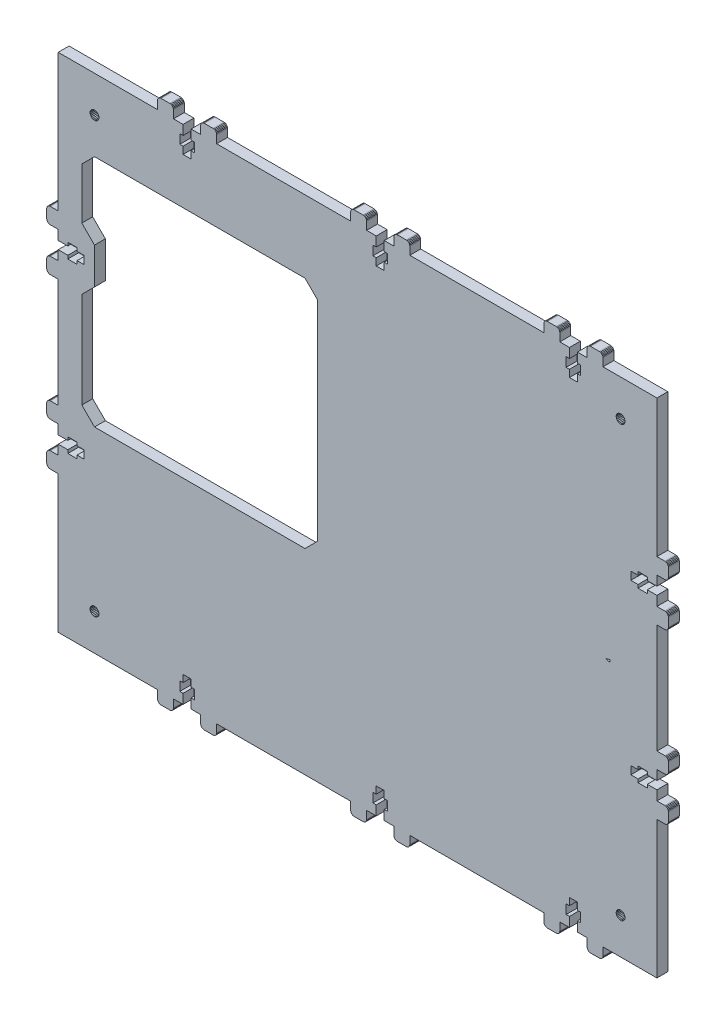
SolidWorks part; units mm, degrees
material "Maple"
ref_plane "Front Plane" through (0, 0, 0) normal (0, 0, 1) x (1, 0, 0)
ref_plane "Top Plane" through (0, 0, 0) normal (0, 1, 0) x (1, 0, 0)
ref_plane "Right Plane" through (0, 0, 0) normal (1, 0, 0) x (0, 0, -1)
sketch "Sketch1" plane through (0, 0, 0) normal (0, 0, 1) x (1, 0, 0)
  line L4138 (-90.633, 287.9777) -> (-85.333, 287.9777)
  line L4139 (-95.733, 287.9777) -> (-95.733, 286.1777)
  line L4140 (-90.633, 286.1777) -> (-90.633, 287.9777)
  line L4141 (-90.633, 294.1777) -> (-95.733, 294.1777)
  line L4142 (-415.2329, 189.8778) -> (-415.2329, 195.1777)
  line L4143 (-95.733, 292.3777) -> (-99.683, 292.3777)
  line L4144 (-147.633, 105.3778) -> (-221.483, 105.3778)
  line L4145 (-346.4329, 376.8777) -> (-348.2329, 376.8777)
  line L4146 (-342.0329, 367.8277) -> (-342.0329, 371.7777)
  line L4147 (-348.2329, 371.7777) -> (-346.4329, 371.7777)
  line L4148 (-336.7329, 382.1777) -> (-336.7329, 386.5277)
  line L4149 (-360.5329, 382.1777) -> (-360.5329, 386.5277)
  line L4150 (-340.2329, 371.7777) -> (-340.2329, 376.8777)
  line L4151 (-346.4329, 367.8277) -> (-342.0329, 367.8277)
  line L4152 (-90.633, 195.1777) -> (-85.333, 195.1777)
  line L4153 (-254.083, 105.3778) -> (-327.933, 105.3778)
  line L4154 (-85.333, 199.5777) -> (-90.633, 199.5777)
  line L4155 (-129.133, 371.7777) -> (-127.333, 371.7777)
  line L4156 (-95.733, 195.1777) -> (-95.733, 193.3777)
  line L4157 (-85.333, 292.3777) -> (-90.633, 292.3777)
  line L4158 (-133.533, 367.8277) -> (-129.133, 367.8277)
  line L4159 (-90.633, 201.3777) -> (-95.733, 201.3777)
  line L4160 (-340.2329, 376.8777) -> (-342.0329, 376.8777)
  line L4161 (-348.2329, 376.8777) -> (-348.2329, 371.7777)
  line L4162 (-415.2329, 382.1777) -> (-360.5329, 382.1777)
  line L4163 (-135.333, 371.7777) -> (-133.533, 371.7777)
  line L4164 (-415.2329, 105.3778) -> (-415.2329, 181.0778)
  line L4165 (-239.983, 371.7777) -> (-239.983, 367.8277)
  line L4166 (-235.583, 367.8277) -> (-235.583, 371.7777)
  line L4167 (-127.333, 110.6778) -> (-127.333, 115.7778)
  line L4168 (-129.133, 110.6778) -> (-127.333, 110.6778)
  line L4169 (-133.533, 119.7278) -> (-133.533, 115.7778)
  line L4170 (-135.333, 376.8777) -> (-135.333, 371.7777)
  line L4171 (-409.9329, 286.1777) -> (-404.8329, 286.1777)
  line L4172 (-409.9329, 287.9777) -> (-409.9329, 286.1777)
  line L4173 (-400.8829, 292.3777) -> (-404.8329, 292.3777)
  line L4174 (-404.8329, 286.1777) -> (-404.8329, 287.9777)
  line L4175 (-415.2329, 297.6777) -> (-419.5829, 297.6777)
  line L4176 (-415.2329, 273.8777) -> (-419.5829, 273.8777)
  line L4177 (-404.8329, 294.1777) -> (-409.9329, 294.1777)
  line L4178 (-230.283, 382.1777) -> (-230.283, 386.5277)
  line L4179 (-360.5329, 105.3778) -> (-415.2329, 105.3778)
  line L4180 (-409.9329, 292.3777) -> (-415.2329, 292.3777)
  line L4181 (-404.8329, 292.3777) -> (-404.8329, 294.1777)
  line L4182 (-409.9329, 294.1777) -> (-409.9329, 292.3777)
  line L4183 (-115.033, 382.1777) -> (-85.333, 382.1777)
  line L4184 (-239.983, 382.1777) -> (-239.983, 376.8777)
  line L4185 (-235.583, 376.8777) -> (-235.583, 382.1777)
  line L4186 (-241.783, 376.8777) -> (-241.783, 371.7777)
  line L4187 (-409.9329, 193.3777) -> (-404.8329, 193.3777)
  line L4188 (-409.9329, 195.1777) -> (-409.9329, 193.3777)
  line L4189 (-400.8829, 199.5777) -> (-404.8329, 199.5777)
  line L4190 (-127.333, 115.7778) -> (-129.133, 115.7778)
  line L4191 (-138.833, 105.3778) -> (-138.833, 101.0278)
  line L4192 (-115.033, 105.3778) -> (-115.033, 101.0278)
  line L4193 (-135.333, 115.7778) -> (-135.333, 110.6778)
  line L4194 (-129.133, 119.7278) -> (-133.533, 119.7278)
  line L4195 (-346.4329, 119.7278) -> (-346.4329, 115.7778)
  line L4196 (-235.583, 119.7278) -> (-239.983, 119.7278)
  line L4197 (-415.2329, 306.4777) -> (-415.2329, 382.1777)
  line L4198 (-235.583, 105.3778) -> (-235.583, 110.6778)
  line L4199 (-133.533, 105.3778) -> (-138.833, 105.3778)
  line L4200 (-123.833, 105.3778) -> (-129.133, 105.3778)
  line L4201 (-133.533, 115.7778) -> (-135.333, 115.7778)
  line L4202 (-135.333, 110.6778) -> (-133.533, 110.6778)
  line L4203 (-235.583, 115.7778) -> (-235.583, 119.7278)
  line L4204 (-230.283, 105.3778) -> (-235.583, 105.3778)
  line L4205 (-90.633, 193.3777) -> (-90.633, 195.1777)
  line L4206 (-346.4329, 110.6778) -> (-346.4329, 105.3778)
  line L4207 (-346.4329, 115.7778) -> (-348.2329, 115.7778)
  line L4208 (-85.333, 213.6777) -> (-80.983, 213.6777)
  line L4209 (-95.733, 193.3777) -> (-90.633, 193.3777)
  line L4210 (-90.633, 199.5777) -> (-90.633, 201.3777)
  line L4211 (-342.0329, 376.8777) -> (-342.0329, 382.1777)
  line L4212 (-342.0329, 371.7777) -> (-340.2329, 371.7777)
  line L4213 (-351.7329, 105.3778) -> (-351.7329, 101.0278)
  line L4214 (-327.933, 105.3778) -> (-327.933, 101.0278)
  line L4215 (-348.2329, 115.7778) -> (-348.2329, 110.6778)
  line L4216 (-127.333, 371.7777) -> (-127.333, 376.8777)
  line L4217 (-415.2329, 195.1777) -> (-409.9329, 195.1777)
  line L4218 (-235.583, 382.1777) -> (-230.283, 382.1777)
  line L4219 (-241.783, 371.7777) -> (-239.983, 371.7777)
  line L4220 (-239.983, 376.8777) -> (-241.783, 376.8777)
  line L4221 (-346.4329, 382.1777) -> (-346.4329, 376.8777)
  line L4222 (-346.4329, 371.7777) -> (-346.4329, 367.8277)
  line L4223 (-239.983, 110.6778) -> (-239.983, 105.3778)
  line L4224 (-239.983, 115.7778) -> (-241.783, 115.7778)
  line L4225 (-241.783, 110.6778) -> (-239.983, 110.6778)
  line L4226 (-233.783, 110.6778) -> (-233.783, 115.7778)
  line L4227 (-415.2329, 292.3777) -> (-415.2329, 297.6777)
  line L4228 (-415.2329, 199.5777) -> (-415.2329, 204.8777)
  line L4229 (-133.533, 376.8777) -> (-135.333, 376.8777)
  line L4230 (-404.8329, 193.3777) -> (-404.8329, 195.1777)
  line L4231 (-415.2329, 287.9777) -> (-409.9329, 287.9777)
  line L4232 (-404.8329, 287.9777) -> (-400.8829, 287.9777)
  line L4233 (-415.2329, 282.6777) -> (-415.2329, 287.9777)
  line L4234 (-239.983, 367.8277) -> (-235.583, 367.8277)
  line L4235 (-233.783, 376.8777) -> (-235.583, 376.8777)
  line L4236 (-233.783, 371.7777) -> (-233.783, 376.8777)
  line L4237 (-346.4329, 105.3778) -> (-351.7329, 105.3778)
  line L4238 (-340.2329, 110.6778) -> (-340.2329, 115.7778)
  line L4239 (-90.633, 292.3777) -> (-90.633, 294.1777)
  line L4240 (-99.683, 287.9777) -> (-95.733, 287.9777)
  line L4241 (-95.733, 294.1777) -> (-95.733, 292.3777)
  line L4242 (-85.333, 282.6777) -> (-80.983, 282.6777)
  line L4243 (-85.333, 195.1777) -> (-85.333, 189.8777)
  line L4244 (-400.8829, 287.9777) -> (-400.8829, 292.3777)
  line L4245 (-133.533, 382.1777) -> (-133.533, 376.8777)
  line L4246 (-133.533, 371.7777) -> (-133.533, 367.8277)
  line L4247 (-129.133, 367.8277) -> (-129.133, 371.7777)
  line L4248 (-342.0329, 382.1777) -> (-336.7329, 382.1777)
  line L4249 (-327.9329, 382.1777) -> (-254.083, 382.1777)
  line L4250 (-221.483, 382.1777) -> (-147.633, 382.1777)
  line L4251 (-351.7329, 382.1777) -> (-346.4329, 382.1777)
  line L4252 (-404.8329, 201.3777) -> (-409.9329, 201.3777)
  line L4253 (-400.8829, 195.1777) -> (-400.8829, 199.5777)
  line L4254 (-409.9329, 199.5777) -> (-415.2329, 199.5777)
  line L4255 (-239.983, 119.7278) -> (-239.983, 115.7778)
  line L4256 (-233.783, 115.7778) -> (-235.583, 115.7778)
  line L4257 (-245.283, 105.3778) -> (-245.283, 101.0278)
  line L4258 (-221.483, 105.3778) -> (-221.483, 101.0278)
  line L4259 (-241.783, 115.7778) -> (-241.783, 110.6778)
  line L4260 (-95.733, 286.1777) -> (-90.633, 286.1777)
  line L4261 (-99.683, 292.3777) -> (-99.683, 287.9777)
  line L4262 (-415.2329, 204.8777) -> (-419.5829, 204.8777)
  line L4263 (-415.2329, 181.0778) -> (-419.5829, 181.0778)
  line L4264 (-99.683, 195.1777) -> (-95.733, 195.1777)
  line L4265 (-85.333, 189.8777) -> (-80.983, 189.8777)
  line L4266 (-245.283, 382.1777) -> (-239.983, 382.1777)
  line L4267 (-129.133, 105.3778) -> (-129.133, 110.6778)
  line L4268 (-129.133, 115.7778) -> (-129.133, 119.7278)
  line L4269 (-239.983, 105.3778) -> (-245.283, 105.3778)
  line L4270 (-133.533, 110.6778) -> (-133.533, 105.3778)
  line L4271 (-235.583, 371.7777) -> (-233.783, 371.7777)
  line L4272 (-336.7329, 105.3778) -> (-342.0329, 105.3778)
  line L4273 (-404.8329, 195.1777) -> (-400.8829, 195.1777)
  line L4274 (-85.333, 287.9777) -> (-85.333, 282.6777)
  line L4275 (-85.333, 273.8777) -> (-85.333, 213.6777)
  line L4276 (-85.333, 204.8777) -> (-85.333, 199.5777)
  line L4277 (-254.083, 382.1777) -> (-254.083, 386.5277)
  line L4278 (-409.9329, 201.3777) -> (-409.9329, 199.5777)
  line L4279 (-127.333, 376.8777) -> (-129.133, 376.8777)
  line L4280 (-129.133, 376.8777) -> (-129.133, 382.1777)
  line L4281 (-129.133, 382.1777) -> (-123.833, 382.1777)
  line L4282 (-415.2329, 213.6777) -> (-415.2329, 273.8777)
  line L4283 (-123.833, 382.1777) -> (-123.833, 386.5277)
  line L4284 (-85.333, 181.0778) -> (-85.333, 105.3778)
  line L4285 (-85.333, 105.3778) -> (-115.033, 105.3778)
  line L4286 (-95.733, 201.3777) -> (-95.733, 199.5777)
  line L4287 (-95.733, 199.5777) -> (-99.683, 199.5777)
  line L4288 (-99.683, 199.5777) -> (-99.683, 195.1777)
  line L4289 (-342.0329, 105.3778) -> (-342.0329, 110.6778)
  line L4290 (-342.0329, 110.6778) -> (-340.2329, 110.6778)
  line L4291 (-340.2329, 115.7778) -> (-342.0329, 115.7778)
  line L4292 (-342.0329, 115.7778) -> (-342.0329, 119.7278)
  line L4293 (-342.0329, 119.7278) -> (-346.4329, 119.7278)
  line L4294 (-404.8329, 199.5777) -> (-404.8329, 201.3777)
  line L4295 (-85.333, 382.1777) -> (-85.333, 306.4777)
  line L4296 (-85.333, 306.4777) -> (-80.983, 306.4777)
  line L4297 (-78.983, 299.6777) -> (-79.0512, 299.1601)
  line L4298 (-79.0512, 299.1601) -> (-79.251, 298.6777)
  line L4299 (-79.251, 298.6777) -> (-79.5688, 298.2635)
  line L4300 (-79.5688, 298.2635) -> (-79.983, 297.9457)
  line L4301 (-79.983, 297.9457) -> (-80.4654, 297.7459)
  line L4302 (-80.983, 297.6777) -> (-85.333, 297.6777)
  line L4303 (-80.4654, 297.7459) -> (-80.983, 297.6777)
  line L4304 (-80.983, 282.6777) -> (-80.4654, 282.6096)
  line L4305 (-80.4654, 282.6096) -> (-79.983, 282.4098)
  line L4306 (-79.983, 282.4098) -> (-79.5688, 282.0919)
  line L4307 (-79.5688, 282.0919) -> (-79.251, 281.6777)
  line L4308 (-79.251, 281.6777) -> (-79.0512, 281.1954)
  line L4309 (-78.983, 280.6777) -> (-78.983, 275.8777)
  line L4310 (-79.0512, 281.1954) -> (-78.983, 280.6777)
  line L4311 (-80.983, 273.8777) -> (-85.333, 273.8777)
  line L4312 (-80.983, 273.8777) -> (-80.4654, 273.9459)
  line L4313 (-80.4654, 273.9459) -> (-79.983, 274.1457)
  line L4314 (-79.983, 274.1457) -> (-79.5688, 274.4635)
  line L4315 (-79.5688, 274.4635) -> (-79.251, 274.8777)
  line L4316 (-79.251, 274.8777) -> (-79.0512, 275.3601)
  line L4317 (-79.0512, 275.3601) -> (-78.983, 275.8777)
  line L4318 (-80.983, 306.4777) -> (-80.4654, 306.4096)
  line L4319 (-80.4654, 306.4096) -> (-79.983, 306.2098)
  line L4320 (-79.983, 306.2098) -> (-79.5688, 305.8919)
  line L4321 (-79.5688, 305.8919) -> (-79.251, 305.4777)
  line L4322 (-79.251, 305.4777) -> (-79.0512, 304.9953)
  line L4323 (-78.983, 304.4777) -> (-78.983, 299.6777)
  line L4324 (-79.0512, 304.9953) -> (-78.983, 304.4777)
  line L4325 (-80.983, 189.8777) -> (-80.4654, 189.8096)
  line L4326 (-80.4654, 189.8096) -> (-79.983, 189.6098)
  line L4327 (-79.983, 189.6098) -> (-79.5688, 189.292)
  line L4328 (-79.5688, 189.292) -> (-79.251, 188.8777)
  line L4329 (-79.251, 188.8777) -> (-79.0512, 188.3954)
  line L4330 (-78.983, 187.8777) -> (-78.983, 183.0778)
  line L4331 (-79.0512, 188.3954) -> (-78.983, 187.8777)
  line L4332 (-80.983, 181.0778) -> (-85.333, 181.0778)
  line L4333 (-80.983, 181.0778) -> (-80.4654, 181.1459)
  line L4334 (-80.4654, 181.1459) -> (-79.983, 181.3457)
  line L4335 (-79.983, 181.3457) -> (-79.5688, 181.6635)
  line L4336 (-79.5688, 181.6635) -> (-79.251, 182.0778)
  line L4337 (-79.251, 182.0778) -> (-79.0512, 182.5601)
  line L4338 (-79.0512, 182.5601) -> (-78.983, 183.0778)
  line L4339 (-80.983, 204.8777) -> (-85.333, 204.8777)
  line L4340 (-80.983, 204.8777) -> (-80.4654, 204.9459)
  line L4341 (-80.4654, 204.9459) -> (-79.983, 205.1457)
  line L4342 (-79.983, 205.1457) -> (-79.5688, 205.4635)
  line L4343 (-79.5688, 205.4635) -> (-79.251, 205.8777)
  line L4344 (-79.251, 205.8777) -> (-79.0512, 206.3601)
  line L4345 (-79.0512, 206.3601) -> (-78.983, 206.8777)
  line L4346 (-80.983, 213.6777) -> (-80.4654, 213.6096)
  line L4347 (-80.4654, 213.6096) -> (-79.983, 213.4098)
  line L4348 (-79.983, 213.4098) -> (-79.5688, 213.092)
  line L4349 (-79.5688, 213.092) -> (-79.251, 212.6777)
  line L4350 (-79.251, 212.6777) -> (-79.0512, 212.1954)
  line L4351 (-78.983, 211.6777) -> (-78.983, 206.8777)
  line L4352 (-79.0512, 212.1954) -> (-78.983, 211.6777)
  line L4353 (-419.5829, 213.6777) -> (-415.2329, 213.6777)
  line L4354 (-419.5829, 213.6777) -> (-420.1006, 213.6096)
  line L4355 (-420.1006, 213.6096) -> (-420.5829, 213.4098)
  line L4356 (-420.5829, 213.4098) -> (-420.9971, 213.092)
  line L4357 (-420.9971, 213.092) -> (-421.315, 212.6777)
  line L4358 (-421.315, 212.6777) -> (-421.5148, 212.1954)
  line L4359 (-421.5148, 212.1954) -> (-421.5829, 211.6777)
  line L4360 (-419.5829, 204.8777) -> (-420.1006, 204.9459)
  line L4361 (-420.1006, 204.9459) -> (-420.5829, 205.1457)
  line L4362 (-420.5829, 205.1457) -> (-420.9971, 205.4635)
  line L4363 (-420.9971, 205.4635) -> (-421.315, 205.8777)
  line L4364 (-421.315, 205.8777) -> (-421.5148, 206.3601)
  line L4365 (-421.5829, 206.8777) -> (-421.5829, 211.6777)
  line L4366 (-421.5148, 206.3601) -> (-421.5829, 206.8777)
  line L4367 (-254.083, 101.0278) -> (-254.083, 105.3778)
  line L4368 (-254.083, 101.0278) -> (-254.0148, 100.5101)
  line L4369 (-254.0148, 100.5101) -> (-253.815, 100.0278)
  line L4370 (-253.815, 100.0278) -> (-253.4972, 99.6136)
  line L4371 (-253.4972, 99.6136) -> (-253.083, 99.2957)
  line L4372 (-253.083, 99.2957) -> (-252.6006, 99.0959)
  line L4373 (-252.6006, 99.0959) -> (-252.083, 99.0278)
  line L4374 (-334.7329, 99.0278) -> (-335.2506, 99.0959)
  line L4375 (-335.2506, 99.0959) -> (-335.7329, 99.2957)
  line L4376 (-335.7329, 99.2957) -> (-336.1472, 99.6136)
  line L4377 (-336.1472, 99.6136) -> (-336.465, 100.0278)
  line L4378 (-336.465, 100.0278) -> (-336.6648, 100.5101)
  line L4379 (-336.7329, 101.0278) -> (-336.7329, 105.3778)
  line L4380 (-336.6648, 100.5101) -> (-336.7329, 101.0278)
  line L4381 (-334.7329, 388.5277) -> (-329.9329, 388.5277)
  line L4382 (-334.7329, 388.5277) -> (-335.2506, 388.4595)
  line L4383 (-335.2506, 388.4595) -> (-335.7329, 388.2597)
  line L4384 (-335.7329, 388.2597) -> (-336.1472, 387.9419)
  line L4385 (-336.1472, 387.9419) -> (-336.465, 387.5277)
  line L4386 (-336.465, 387.5277) -> (-336.6648, 387.0453)
  line L4387 (-336.6648, 387.0453) -> (-336.7329, 386.5277)
  line L4388 (-360.5329, 386.5277) -> (-360.4648, 387.0453)
  line L4389 (-360.4648, 387.0453) -> (-360.265, 387.5277)
  line L4390 (-360.265, 387.5277) -> (-359.9471, 387.9419)
  line L4391 (-359.9471, 387.9419) -> (-359.5329, 388.2597)
  line L4392 (-359.5329, 388.2597) -> (-359.0506, 388.4595)
  line L4393 (-358.5329, 388.5277) -> (-353.7329, 388.5277)
  line L4394 (-359.0506, 388.4595) -> (-358.5329, 388.5277)
  line L4395 (-351.7329, 386.5277) -> (-351.7329, 382.1777)
  line L4396 (-351.7329, 386.5277) -> (-351.8011, 387.0453)
  line L4397 (-351.8011, 387.0453) -> (-352.0009, 387.5277)
  line L4398 (-352.0009, 387.5277) -> (-352.3187, 387.9419)
  line L4399 (-352.3187, 387.9419) -> (-352.7329, 388.2597)
  line L4400 (-352.7329, 388.2597) -> (-353.2153, 388.4595)
  line L4401 (-353.2153, 388.4595) -> (-353.7329, 388.5277)
  line L4402 (-121.833, 388.5277) -> (-117.033, 388.5277)
  line L4403 (-121.833, 388.5277) -> (-122.3506, 388.4595)
  line L4404 (-122.3506, 388.4595) -> (-122.833, 388.2597)
  line L4405 (-122.833, 388.2597) -> (-123.2472, 387.9419)
  line L4406 (-123.2472, 387.9419) -> (-123.5651, 387.5277)
  line L4407 (-123.5651, 387.5277) -> (-123.7649, 387.0453)
  line L4408 (-123.7649, 387.0453) -> (-123.833, 386.5277)
  line L4409 (-358.5329, 99.0278) -> (-359.0506, 99.0959)
  line L4410 (-359.0506, 99.0959) -> (-359.5329, 99.2957)
  line L4411 (-359.5329, 99.2957) -> (-359.9471, 99.6136)
  line L4412 (-359.9471, 99.6136) -> (-360.265, 100.0278)
  line L4413 (-360.265, 100.0278) -> (-360.4648, 100.5101)
  line L4414 (-360.5329, 101.0278) -> (-360.5329, 105.3778)
  line L4415 (-360.4648, 100.5101) -> (-360.5329, 101.0278)
  line L4416 (-421.5829, 299.6777) -> (-421.5829, 304.4777)
  line L4417 (-421.5829, 299.6777) -> (-421.5148, 299.1601)
  line L4418 (-421.5148, 299.1601) -> (-421.315, 298.6777)
  line L4419 (-421.315, 298.6777) -> (-420.9971, 298.2635)
  line L4420 (-420.9971, 298.2635) -> (-420.5829, 297.9457)
  line L4421 (-420.5829, 297.9457) -> (-420.1006, 297.7459)
  line L4422 (-420.1006, 297.7459) -> (-419.5829, 297.6777)
  line L4423 (-419.5829, 306.4777) -> (-415.2329, 306.4777)
  line L4424 (-419.5829, 306.4777) -> (-420.1006, 306.4096)
  line L4425 (-420.1006, 306.4096) -> (-420.5829, 306.2098)
  line L4426 (-420.5829, 306.2098) -> (-420.9971, 305.8919)
  line L4427 (-420.9971, 305.8919) -> (-421.315, 305.4777)
  line L4428 (-421.315, 305.4777) -> (-421.5148, 304.9953)
  line L4429 (-421.5148, 304.9953) -> (-421.5829, 304.4777)
  line L4430 (-327.9329, 386.5277) -> (-327.9329, 382.1777)
  line L4431 (-327.9329, 386.5277) -> (-328.0011, 387.0453)
  line L4432 (-328.0011, 387.0453) -> (-328.2009, 387.5277)
  line L4433 (-328.2009, 387.5277) -> (-328.5187, 387.9419)
  line L4434 (-328.5187, 387.9419) -> (-328.9329, 388.2597)
  line L4435 (-328.9329, 388.2597) -> (-329.4153, 388.4595)
  line L4436 (-329.4153, 388.4595) -> (-329.9329, 388.5277)
  line L4437 (-123.833, 101.0278) -> (-123.833, 105.3778)
  line L4438 (-123.833, 101.0278) -> (-123.7649, 100.5101)
  line L4439 (-123.7649, 100.5101) -> (-123.5651, 100.0278)
  line L4440 (-123.5651, 100.0278) -> (-123.2472, 99.6136)
  line L4441 (-123.2472, 99.6136) -> (-122.833, 99.2957)
  line L4442 (-122.833, 99.2957) -> (-122.3507, 99.0959)
  line L4443 (-122.3507, 99.0959) -> (-121.833, 99.0278)
  line L4444 (-140.833, 99.0278) -> (-145.633, 99.0278)
  line L4445 (-140.833, 99.0278) -> (-140.3154, 99.0959)
  line L4446 (-140.3154, 99.0959) -> (-139.833, 99.2957)
  line L4447 (-139.833, 99.2957) -> (-139.4188, 99.6136)
  line L4448 (-139.4188, 99.6136) -> (-139.101, 100.0278)
  line L4449 (-139.101, 100.0278) -> (-138.9012, 100.5101)
  line L4450 (-138.9012, 100.5101) -> (-138.833, 101.0278)
  line L4451 (-147.633, 101.0278) -> (-147.633, 105.3778)
  line L4452 (-147.633, 101.0278) -> (-147.5649, 100.5101)
  line L4453 (-147.5649, 100.5101) -> (-147.3651, 100.0278)
  line L4454 (-147.3651, 100.0278) -> (-147.0472, 99.6136)
  line L4455 (-147.0472, 99.6136) -> (-146.633, 99.2957)
  line L4456 (-146.633, 99.2957) -> (-146.1506, 99.0959)
  line L4457 (-146.1506, 99.0959) -> (-145.633, 99.0278)
  line L4458 (-421.5829, 275.8777) -> (-421.5829, 280.6777)
  line L4459 (-421.5829, 275.8777) -> (-421.5148, 275.3601)
  line L4460 (-421.5148, 275.3601) -> (-421.315, 274.8777)
  line L4461 (-421.315, 274.8777) -> (-420.9971, 274.4635)
  line L4462 (-420.9971, 274.4635) -> (-420.5829, 274.1457)
  line L4463 (-420.5829, 274.1457) -> (-420.1006, 273.9459)
  line L4464 (-420.1006, 273.9459) -> (-419.5829, 273.8777)
  line L4465 (-228.283, 388.5277) -> (-223.483, 388.5277)
  line L4466 (-228.283, 388.5277) -> (-228.8006, 388.4595)
  line L4467 (-228.8006, 388.4595) -> (-229.283, 388.2597)
  line L4468 (-229.283, 388.2597) -> (-229.6972, 387.9419)
  line L4469 (-229.6972, 387.9419) -> (-230.015, 387.5277)
  line L4470 (-230.015, 387.5277) -> (-230.2148, 387.0453)
  line L4471 (-230.2148, 387.0453) -> (-230.283, 386.5277)
  line L4472 (-419.5829, 282.6777) -> (-415.2329, 282.6777)
  line L4473 (-419.5829, 282.6777) -> (-420.1006, 282.6096)
  line L4474 (-420.1006, 282.6096) -> (-420.5829, 282.4098)
  line L4475 (-420.5829, 282.4098) -> (-420.9971, 282.0919)
  line L4476 (-420.9971, 282.0919) -> (-421.315, 281.6777)
  line L4477 (-421.315, 281.6777) -> (-421.5148, 281.1954)
  line L4478 (-421.5148, 281.1954) -> (-421.5829, 280.6777)
  line L4479 (-221.483, 386.5277) -> (-221.483, 382.1777)
  line L4480 (-221.483, 386.5277) -> (-221.5511, 387.0453)
  line L4481 (-221.5511, 387.0453) -> (-221.7509, 387.5277)
  line L4482 (-221.7509, 387.5277) -> (-222.0688, 387.9419)
  line L4483 (-222.0688, 387.9419) -> (-222.483, 388.2597)
  line L4484 (-222.483, 388.2597) -> (-222.9653, 388.4595)
  line L4485 (-222.9653, 388.4595) -> (-223.483, 388.5277)
  line L4486 (-115.033, 386.5277) -> (-115.033, 382.1777)
  line L4487 (-115.033, 386.5277) -> (-115.1012, 387.0453)
  line L4488 (-115.1012, 387.0453) -> (-115.301, 387.5277)
  line L4489 (-115.301, 387.5277) -> (-115.6188, 387.9419)
  line L4490 (-115.6188, 387.9419) -> (-116.033, 388.2597)
  line L4491 (-116.033, 388.2597) -> (-116.5154, 388.4595)
  line L4492 (-116.5154, 388.4595) -> (-117.033, 388.5277)
  line L4493 (-138.833, 386.5277) -> (-138.833, 382.1777)
  line L4494 (-138.833, 386.5277) -> (-138.9012, 387.0453)
  line L4495 (-138.9012, 387.0453) -> (-139.101, 387.5277)
  line L4496 (-139.101, 387.5277) -> (-139.4188, 387.9419)
  line L4497 (-139.4188, 387.9419) -> (-139.833, 388.2597)
  line L4498 (-139.833, 388.2597) -> (-140.3154, 388.4595)
  line L4499 (-140.3154, 388.4595) -> (-140.833, 388.5277)
  line L4500 (-115.033, 101.0278) -> (-115.1012, 100.5101)
  line L4501 (-115.1012, 100.5101) -> (-115.301, 100.0278)
  line L4502 (-115.301, 100.0278) -> (-115.6188, 99.6136)
  line L4503 (-115.6188, 99.6136) -> (-116.033, 99.2957)
  line L4504 (-116.033, 99.2957) -> (-116.5154, 99.0959)
  line L4505 (-117.033, 99.0278) -> (-121.833, 99.0278)
  line L4506 (-116.5154, 99.0959) -> (-117.033, 99.0278)
  line L4507 (-421.5829, 187.8778) -> (-421.5148, 188.3954)
  line L4508 (-421.5148, 188.3954) -> (-421.315, 188.8778)
  line L4509 (-421.315, 188.8778) -> (-420.9971, 189.292)
  line L4510 (-420.9971, 189.292) -> (-420.5829, 189.6098)
  line L4511 (-420.5829, 189.6098) -> (-420.1006, 189.8096)
  line L4512 (-419.5829, 189.8778) -> (-415.2329, 189.8778)
  line L4513 (-420.1006, 189.8096) -> (-419.5829, 189.8778)
  line L4514 (-353.7329, 99.0278) -> (-358.5329, 99.0278)
  line L4515 (-353.7329, 99.0278) -> (-353.2153, 99.0959)
  line L4516 (-353.2153, 99.0959) -> (-352.7329, 99.2957)
  line L4517 (-352.7329, 99.2957) -> (-352.3187, 99.6136)
  line L4518 (-352.3187, 99.6136) -> (-352.0009, 100.0278)
  line L4519 (-352.0009, 100.0278) -> (-351.8011, 100.5101)
  line L4520 (-351.8011, 100.5101) -> (-351.7329, 101.0278)
  line L4521 (-327.933, 101.0278) -> (-328.0011, 100.5101)
  line L4522 (-328.0011, 100.5101) -> (-328.2009, 100.0278)
  line L4523 (-328.2009, 100.0278) -> (-328.5187, 99.6136)
  line L4524 (-328.5187, 99.6136) -> (-328.933, 99.2957)
  line L4525 (-328.933, 99.2957) -> (-329.4153, 99.0959)
  line L4526 (-329.933, 99.0278) -> (-334.7329, 99.0278)
  line L4527 (-329.4153, 99.0959) -> (-329.933, 99.0278)
  line L4528 (-228.283, 99.0278) -> (-228.8006, 99.0959)
  line L4529 (-228.8006, 99.0959) -> (-229.283, 99.2957)
  line L4530 (-229.283, 99.2957) -> (-229.6972, 99.6136)
  line L4531 (-229.6972, 99.6136) -> (-230.015, 100.0278)
  line L4532 (-230.015, 100.0278) -> (-230.2148, 100.5101)
  line L4533 (-230.283, 101.0278) -> (-230.283, 105.3778)
  line L4534 (-230.2148, 100.5101) -> (-230.283, 101.0278)
  line L4535 (-245.283, 101.0278) -> (-245.3511, 100.5101)
  line L4536 (-245.3511, 100.5101) -> (-245.5509, 100.0278)
  line L4537 (-245.5509, 100.0278) -> (-245.8688, 99.6136)
  line L4538 (-245.8688, 99.6136) -> (-246.283, 99.2957)
  line L4539 (-246.283, 99.2957) -> (-246.7653, 99.0959)
  line L4540 (-247.283, 99.0278) -> (-252.083, 99.0278)
  line L4541 (-246.7653, 99.0959) -> (-247.283, 99.0278)
  line L4542 (-245.283, 386.5277) -> (-245.283, 382.1777)
  line L4543 (-245.283, 386.5277) -> (-245.3511, 387.0453)
  line L4544 (-245.3511, 387.0453) -> (-245.5509, 387.5277)
  line L4545 (-245.5509, 387.5277) -> (-245.8688, 387.9419)
  line L4546 (-245.8688, 387.9419) -> (-246.283, 388.2597)
  line L4547 (-246.283, 388.2597) -> (-246.7653, 388.4595)
  line L4548 (-246.7653, 388.4595) -> (-247.283, 388.5277)
  line L4549 (-421.5829, 183.0778) -> (-421.5829, 187.8778)
  line L4550 (-421.5829, 183.0778) -> (-421.5148, 182.5601)
  line L4551 (-421.5148, 182.5601) -> (-421.315, 182.0778)
  line L4552 (-421.315, 182.0778) -> (-420.9971, 181.6635)
  line L4553 (-420.9971, 181.6635) -> (-420.5829, 181.3457)
  line L4554 (-420.5829, 181.3457) -> (-420.1006, 181.1459)
  line L4555 (-420.1006, 181.1459) -> (-419.5829, 181.0778)
  line L4556 (-221.483, 101.0278) -> (-221.5511, 100.5101)
  line L4557 (-221.5511, 100.5101) -> (-221.7509, 100.0278)
  line L4558 (-221.7509, 100.0278) -> (-222.0688, 99.6136)
  line L4559 (-222.0688, 99.6136) -> (-222.483, 99.2957)
  line L4560 (-222.483, 99.2957) -> (-222.9653, 99.0959)
  line L4561 (-223.483, 99.0278) -> (-228.283, 99.0278)
  line L4562 (-222.9653, 99.0959) -> (-223.483, 99.0278)
  line L4563 (-252.083, 388.5277) -> (-247.283, 388.5277)
  line L4564 (-252.083, 388.5277) -> (-252.6006, 388.4595)
  line L4565 (-252.6006, 388.4595) -> (-253.083, 388.2597)
  line L4566 (-253.083, 388.2597) -> (-253.4972, 387.9419)
  line L4567 (-253.4972, 387.9419) -> (-253.815, 387.5277)
  line L4568 (-253.815, 387.5277) -> (-254.0148, 387.0453)
  line L4569 (-254.0148, 387.0453) -> (-254.083, 386.5277)
  line L4570 (-145.633, 388.5277) -> (-140.833, 388.5277)
  line L4571 (-145.633, 388.5277) -> (-146.1506, 388.4595)
  line L4572 (-146.1506, 388.4595) -> (-146.633, 388.2597)
  line L4573 (-146.633, 388.2597) -> (-147.0472, 387.9419)
  line L4574 (-147.0472, 387.9419) -> (-147.3651, 387.5277)
  line L4575 (-147.3651, 387.5277) -> (-147.5649, 387.0453)
  line L4576 (-147.5649, 387.0453) -> (-147.633, 386.5277)
  line L4577 (-147.633, 382.1777) -> (-147.633, 386.5277)
  line L4578 (-235.583, 110.6778) -> (-233.783, 110.6778)
  line L4579 (-138.833, 382.1777) -> (-133.533, 382.1777)
  line L4580 (-85.333, 297.6777) -> (-85.333, 292.3777)
  line L4581 (-348.2329, 110.6778) -> (-346.4329, 110.6778)
  line L4582 (-396.4579, 123.256) -> (-395.867, 123.0113)
  line L4583 (-395.867, 123.0113) -> (-395.2329, 122.9278)
  line L4584 (-395.2329, 359.7277) -> (-394.5988, 359.8112)
  line L4585 (-394.5988, 359.8112) -> (-394.0079, 360.0559)
  line L4586 (-394.0079, 360.0559) -> (-393.5005, 360.4453)
  line L4587 (-393.5005, 360.4453) -> (-393.1112, 360.9527)
  line L4588 (-393.1112, 360.9527) -> (-392.8664, 361.5436)
  line L4589 (-392.8664, 361.5436) -> (-392.7829, 362.1777)
  line L4590 (-392.7829, 362.1777) -> (-392.8664, 362.8118)
  line L4591 (-392.8664, 362.8118) -> (-393.1112, 363.4027)
  line L4592 (-393.1112, 363.4027) -> (-393.5005, 363.9101)
  line L4593 (-393.5005, 363.9101) -> (-394.0079, 364.2995)
  line L4594 (-394.0079, 364.2995) -> (-394.5988, 364.5442)
  line L4595 (-394.5988, 364.5442) -> (-395.2329, 364.6277)
  line L4596 (-395.2329, 364.6277) -> (-395.867, 364.5442)
  line L4597 (-395.867, 364.5442) -> (-396.4579, 364.2995)
  line L4598 (-396.4579, 364.2995) -> (-396.9653, 363.9101)
  line L4599 (-396.9653, 363.9101) -> (-397.3547, 363.4027)
  line L4600 (-397.3547, 363.4027) -> (-397.5994, 362.8118)
  line L4601 (-397.5994, 362.8118) -> (-397.6829, 362.1777)
  line L4602 (-393.1112, 124.1528) -> (-392.8664, 124.7437)
  line L4603 (-392.8664, 124.7437) -> (-392.7829, 125.3778)
  line L4604 (-392.7829, 125.3778) -> (-392.8664, 126.0119)
  line L4605 (-392.8664, 126.0119) -> (-393.1112, 126.6028)
  line L4606 (-393.1112, 126.6028) -> (-393.5005, 127.1102)
  line L4607 (-393.5005, 127.1102) -> (-394.0079, 127.4995)
  line L4608 (-394.0079, 127.4995) -> (-394.5988, 127.7443)
  line L4609 (-394.5988, 127.7443) -> (-395.2329, 127.8278)
  line L4610 (-395.2329, 127.8278) -> (-395.867, 127.7443)
  line L4611 (-395.867, 127.7443) -> (-396.4579, 127.4995)
  line L4612 (-396.4579, 127.4995) -> (-396.9653, 127.1102)
  line L4613 (-396.9653, 127.1102) -> (-397.3547, 126.6028)
  line L4614 (-397.3547, 126.6028) -> (-397.5994, 126.0119)
  line L4615 (-397.5994, 126.0119) -> (-397.6829, 125.3778)
  line L4616 (-397.6829, 125.3778) -> (-397.5994, 124.7437)
  line L4617 (-397.5994, 124.7437) -> (-397.3547, 124.1528)
  line L4618 (-397.3547, 124.1528) -> (-396.9653, 123.6454)
  line L4619 (-396.9653, 123.6454) -> (-396.4579, 123.256)
  line L4620 (-393.5005, 123.6454) -> (-393.1112, 124.1528)
  line L4621 (-394.0079, 123.256) -> (-393.5005, 123.6454)
  line L4622 (-394.5988, 123.0113) -> (-394.0079, 123.256)
  line L4623 (-395.2329, 122.9278) -> (-394.5988, 123.0113)
  line L4624 (-395.867, 359.8112) -> (-395.2329, 359.7277)
  line L4625 (-396.4579, 360.0559) -> (-395.867, 359.8112)
  line L4626 (-396.9653, 360.4453) -> (-396.4579, 360.0559)
  line L4627 (-397.3547, 360.9527) -> (-396.9653, 360.4453)
  line L4628 (-397.5994, 361.5436) -> (-397.3547, 360.9527)
  line L4629 (-397.6829, 362.1777) -> (-397.5994, 361.5436)
  line L4630 (-105.333, 359.7277) -> (-105.9671, 359.8112)
  line L4631 (-105.9671, 359.8112) -> (-106.558, 360.0559)
  line L4632 (-106.558, 360.0559) -> (-107.0654, 360.4453)
  line L4633 (-107.0654, 360.4453) -> (-107.4548, 360.9527)
  line L4634 (-107.4548, 360.9527) -> (-107.6995, 361.5436)
  line L4635 (-107.6995, 361.5436) -> (-107.783, 362.1777)
  line L4636 (-107.783, 362.1777) -> (-107.6995, 362.8118)
  line L4637 (-107.6995, 362.8118) -> (-107.4548, 363.4027)
  line L4638 (-107.4548, 363.4027) -> (-107.0654, 363.9101)
  line L4639 (-107.0654, 363.9101) -> (-106.558, 364.2995)
  line L4640 (-106.558, 364.2995) -> (-105.9671, 364.5442)
  line L4641 (-105.9671, 364.5442) -> (-105.333, 364.6277)
  line L4642 (-105.333, 364.6277) -> (-104.6989, 364.5442)
  line L4643 (-104.6989, 364.5442) -> (-104.108, 364.2995)
  line L4644 (-104.108, 364.2995) -> (-103.6006, 363.9101)
  line L4645 (-103.6006, 363.9101) -> (-103.2113, 363.4027)
  line L4646 (-103.2113, 363.4027) -> (-102.9665, 362.8118)
  line L4647 (-102.9665, 362.8118) -> (-102.883, 362.1777)
  line L4648 (-102.883, 362.1777) -> (-102.9665, 361.5436)
  line L4649 (-102.9665, 361.5436) -> (-103.2113, 360.9527)
  line L4650 (-103.2113, 360.9527) -> (-103.6006, 360.4453)
  line L4651 (-103.6006, 360.4453) -> (-104.108, 360.0559)
  line L4652 (-104.108, 360.0559) -> (-104.6989, 359.8112)
  line L4653 (-104.6989, 359.8112) -> (-105.333, 359.7277)
  line L4654 (-105.333, 122.9278) -> (-105.9671, 123.0113)
  line L4655 (-105.9671, 123.0113) -> (-106.558, 123.256)
  line L4656 (-106.558, 123.256) -> (-107.0654, 123.6454)
  line L4657 (-107.0654, 123.6454) -> (-107.4548, 124.1528)
  line L4658 (-107.4548, 124.1528) -> (-107.6995, 124.7437)
  line L4659 (-107.6995, 124.7437) -> (-107.783, 125.3778)
  line L4660 (-107.783, 125.3778) -> (-107.6995, 126.0119)
  line L4661 (-107.6995, 126.0119) -> (-107.4548, 126.6028)
  line L4662 (-107.4548, 126.6028) -> (-107.0654, 127.1102)
  line L4663 (-107.0654, 127.1102) -> (-106.558, 127.4995)
  line L4664 (-106.558, 127.4995) -> (-105.9671, 127.7443)
  line L4665 (-105.9671, 127.7443) -> (-105.333, 127.8278)
  line L4666 (-105.333, 127.8278) -> (-104.6989, 127.7443)
  line L4667 (-104.6989, 127.7443) -> (-104.108, 127.4995)
  line L4668 (-104.108, 127.4995) -> (-103.6006, 127.1102)
  line L4669 (-103.6006, 127.1102) -> (-103.2113, 126.6028)
  line L4670 (-103.2113, 126.6028) -> (-102.9665, 126.0119)
  line L4671 (-102.9665, 126.0119) -> (-102.883, 125.3778)
  line L4672 (-102.883, 125.3778) -> (-102.9665, 124.7437)
  line L4673 (-102.9665, 124.7437) -> (-103.2113, 124.1528)
  line L4674 (-103.2113, 124.1528) -> (-103.6006, 123.6454)
  line L4675 (-103.6006, 123.6454) -> (-104.108, 123.256)
  line L4676 (-104.108, 123.256) -> (-104.6989, 123.0113)
  line L4677 (-104.6989, 123.0113) -> (-105.333, 122.9278)
  line L4678 (-272.2294, 335.3777) -> (-272.2294, 220.3777)
  line L4679 (-279.2294, 213.3777) -> (-395.2294, 213.3777)
  line L4680 (-395.2294, 300.1777) -> (-395.2294, 280.1777)
  line L4681 (-402.2294, 307.1777) -> (-402.2294, 335.3777)
  line L4682 (-402.2294, 307.1777) -> (-395.2294, 300.1777)
  line L4683 (-395.2294, 280.1777) -> (-402.2294, 273.1777)
  line L4684 (-395.2294, 342.3777) -> (-279.2294, 342.3777)
  line L4685 (-395.2294, 342.3777) -> (-402.2294, 335.3777)
  line L4686 (-402.2294, 220.3777) -> (-402.2294, 273.1777)
  line L4687 (-395.2294, 213.3777) -> (-402.2294, 220.3777)
  line L4688 (-272.2294, 335.3777) -> (-279.2294, 342.3777)
  line L4689 (-272.2294, 220.3777) -> (-279.2294, 213.3777)
  line L9286 (-111.1547, 243.0768) -> (-113.646, 243.6887)
  line L9287 (-113.646, 243.6887) -> (-111.1547, 244.3381)
  line L9288 (-111.1547, 244.3381) -> (-111.1547, 243.0768)
  line L9289 (-109.332, 244.8126) -> (-113.646, 243.6887)
  line L9290 (-113.646, 243.6887) -> (-109.332, 242.6272)
  line L9291 (-109.332, 242.6272) -> (-111.1489, 243.0768)
  line L9292 (-111.1489, 243.0768) -> (-111.1489, 244.3381)
  line L9293 (-111.1489, 244.3381) -> (-109.332, 244.8126)
extrude "Boss-Extrude1" add sketch "Sketch1" along normal blind 6 contours L4581 L4215 L4207 L4195 L4293 L4292 L4291 L4238 L4290 L4289 L4272 L4379 L4380 L4378 L4377 L4376 L4375 L4374 L4526 L4527 L4525 L4524 L4523 L4522 L4521 L4214 L4153 L4367 L4368 L4369 L4370 L4371 L4372 L4373 L4540 L4541 L4539 L4538 L4537 L4536 L4535 L4257 L4269 L4223 L4225 L4259 L4224 L4255 L4196 L4203 L4256
